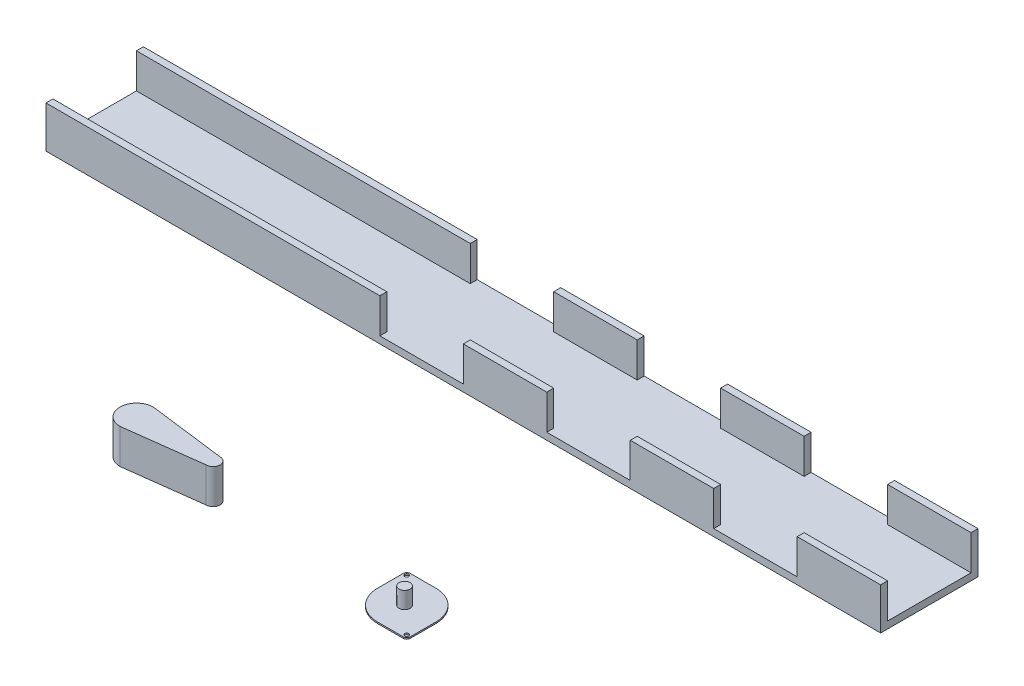
SolidWorks part; units mm, degrees
ref_plane "Front Plane" through (0, 0, 0) normal (0, 0, 1) x (1, 0, 0)
ref_plane "Top Plane" through (0, 0, 0) normal (0, 1, 0) x (1, 0, 0)
ref_plane "Right Plane" through (0, 0, 0) normal (1, 0, 0) x (0, 0, -1)
sketch "Sketch1" plane through (0, 0, 0) normal (0, 1, 0) x (1, 0, 0)
  line L1 (-300, -35) -> (300, -35)
  line L2 (-300, -35) -> (-300, 35)
  line L3 (-300, 35) -> (300, 35)
  line L4 (300, -35) -> (300, 35)
  line L5 (-300, -35) -> (300, 35) construction
  line L6 (-300, 35) -> (300, -35) construction
  point P0 (0, 0)
  dimension "D1" = 600
  dimension "D2" = 70
extrude "Boss-Extrude1" add sketch "Sketch1" along normal blind 30
sketch "Sketch3" plane through (-300, 0, 0) normal (-1, 0, 0) x (0, 0, 1)
  line L0 (35, 30) -> (-35, 30) construction
  line L1 (30, 30) -> (-30, 30)
  line L2 (30, 30) -> (30, 5)
  line L3 (30, 5) -> (-30, 5)
  line L4 (-30, 30) -> (-30, 5)
  line L5 (-35, 30) -> (-35, 0) construction
  dimension "D1" = 60
  dimension "D2" = 25
  dimension "D3" = 5
extrude "Cut-Extrude2" cut sketch "Sketch3" against normal blind 600
sketch "Sketch4" plane through (0, 0, 35) normal (0, 0, 1) x (1, 0, 0)
  line L0 (-300, 30) -> (300, 30) construction
  line L1 (180, 30) -> (240, 30)
  line L2 (180, 30) -> (180, 5)
  line L3 (180, 5) -> (240, 5)
  line L4 (240, 30) -> (240, 5)
  line L5 (300, 30) -> (300, 0) construction
  dimension "D1" = 25
  dimension "D2" = 60
  dimension "D3" = 60
extrude "Cut-Extrude3" cut sketch "Sketch4" against normal blind 70 contours L2 L1 L4 L3
sketch "Sketch10" plane through (0, 0, 35) normal (0, 0, 1) x (1, 0, 0)
  line L0 (-300, 30) -> (180, 30) construction
  line L1 (60, 30) -> (120, 30)
  line L2 (60, 30) -> (60, 5)
  line L3 (60, 5) -> (120, 5)
  line L4 (120, 30) -> (120, 5)
  line L5 (180, 30) -> (180, 5) construction
  line L6 (-60, 30) -> (0, 30)
  line L7 (-60, 30) -> (-60, 5)
  line L8 (-60, 5) -> (0, 5)
  line L9 (0, 30) -> (0, 5)
  dimension "D1" = 60
  dimension "D2" = 25
  dimension "D3" = 60
  dimension "D4" = 60
  dimension "D5" = 25
extrude "Cut-Extrude5" cut sketch "Sketch10" against normal blind 70
sketch "Sketch11" plane through (0, 0, 0) normal (0, 1, 0) x (1, 0, 0)
  line L0 (-77.0998, -180.7463) -> (-22.0998, -187.7463)
  line L1 (-77.0998, -204.7463) -> (-22.0998, -197.7463)
  line L5 (-119.2354, -192.7463) -> (17.6433, -192.7463) construction
  line L6 (-77.0998, -141.6997) -> (-77.0998, -248.2721) construction
  line L7 (-22.0998, -157.664) -> (-22.0998, -232.3078) construction
  arc A0 (-77.0998, -180.7463) -> (-77.0998, -204.7463) centre (-77.0998, -192.7463) ccw
  arc A1 (-22.0998, -197.7463) -> (-22.0998, -187.7463) centre (-22.0998, -192.7463) ccw
  point P14 (0, 0)
extrude "Boss-Extrude4" add sketch "Sketch11" along normal blind 25 separate body
sketch "Sketch13" plane through (0, 0, 0) normal (0, 1, 0) x (1, 0, 0)
  line L0 (92.2732, -209.9422) -> (134.2732, -167.9422) construction
  line L1 (94.762, -167.9422) -> (113.2732, -167.9422)
  line L2 (92.2732, -170.431) -> (92.2732, -188.9422)
  line L3 (113.2732, -209.9422) -> (131.7844, -209.9422)
  line L4 (134.2732, -188.9422) -> (134.2732, -207.4534)
  line L5 (93.0021, -168.6712) -> (134.2732, -209.9422) construction
  arc A0 (134.2732, -188.9422) -> (113.2732, -167.9422) centre (113.2732, -188.9422) ccw
  arc A1 (94.762, -167.9422) -> (92.2732, -170.431) centre (94.762, -170.431) ccw
  circle A2 centre (94.762, -170.431) radius 1.5
  arc A3 (134.2732, -207.4534) -> (131.7844, -209.9422) centre (131.7844, -207.4534) cw
  circle A4 centre (131.7844, -207.4534) radius 1.5
  arc A5 (92.2732, -188.9422) -> (113.2732, -209.9422) centre (113.2732, -188.9422) ccw
  dimension "D1" = 42
  dimension "D2" = 42
extrude "Boss-Extrude5" add sketch "Sketch13" along normal blind 1 separate body
sketch "Sketch14" plane through (0, 1, 0) normal (0, 1, 0) x (1, 0, 0)
  circle A0 centre (112.5311, -189.7565) radius 4
extrude "Boss-Extrude6" add sketch "Sketch14" along normal blind 12
